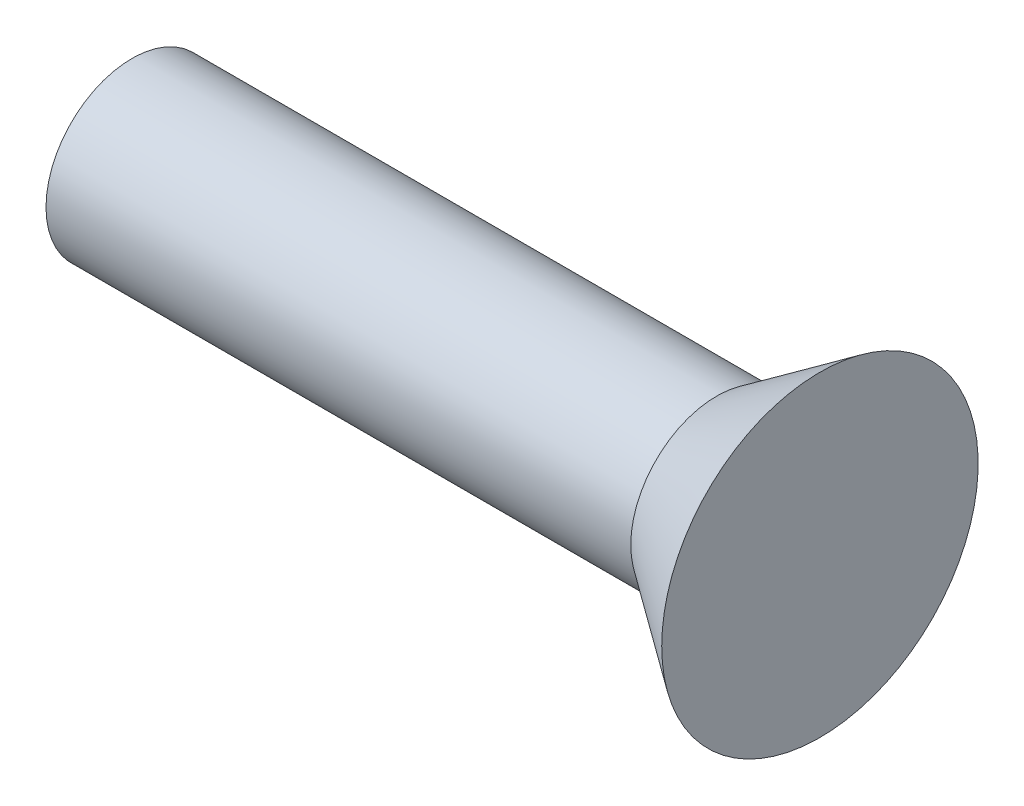
SolidWorks part; units mm, degrees
material "1060 合金"
ref_plane "前视基准面" through (0, 0, 0) normal (0, 0, 1) x (1, 0, 0)
ref_plane "上视基准面" through (0, 0, 0) normal (0, 1, 0) x (1, 0, 0)
ref_plane "右视基准面" through (0, 0, 0) normal (1, 0, 0) x (0, 0, -1)
sketch "草图1" plane through (0, 0, 0) normal (0, 0, 1) x (1, 0, 0)
  line L0 (-53.8441, 0) -> (16.0999, 0) construction
  line L1 (0, 0) -> (0, 1.25)
  line L2 (0, 1.25) -> (8.5, 1.25)
  line L3 (8.5, 1.25) -> (10, 2.3)
  line L4 (0, 0) -> (10, 0)
  line L5 (10, 2.3) -> (10, 0)
  dimension "D1" = 2.5
  dimension "D2" = 10
  dimension "D3" = 1.5
  dimension "D4" = 4.6
  dimension "D5" = 10
revolve "旋转1" add sketch "草图1" angle 360 about L0
cosmetic thread "装饰螺纹线1" parameters "D2"=2.013
